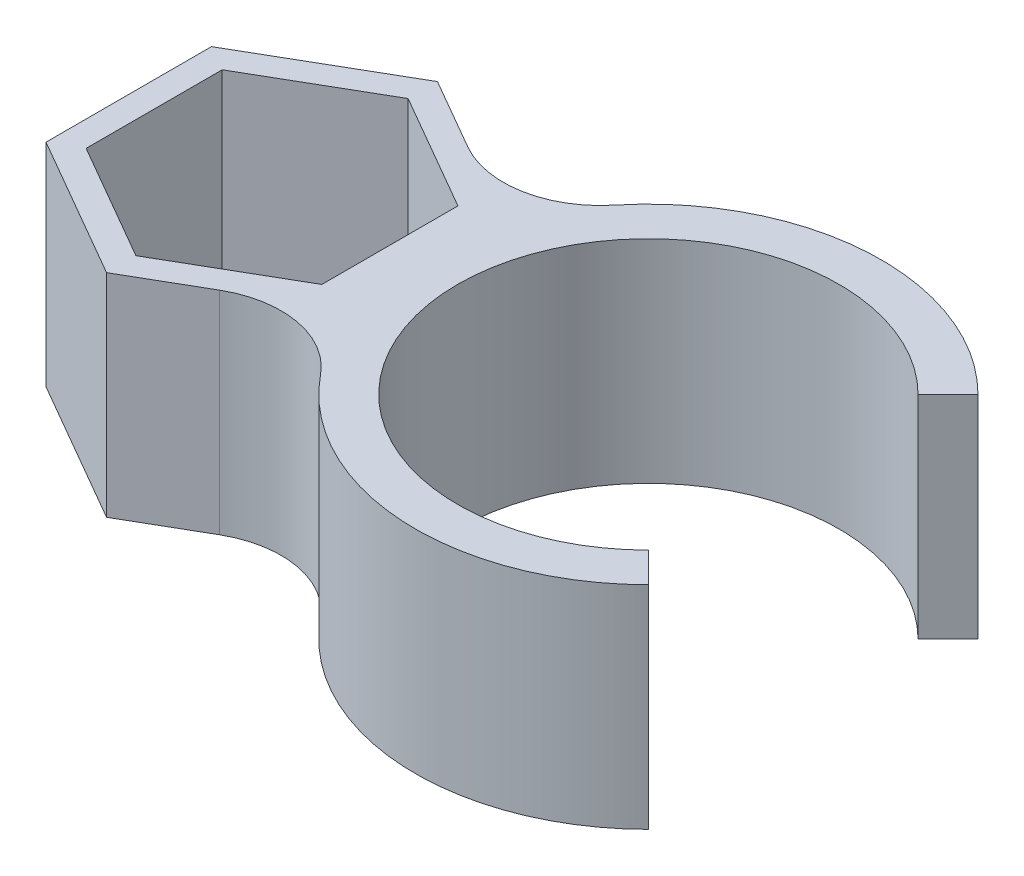
SolidWorks part; units mm, degrees
ref_plane "Front Plane" through (0, 0, 0) normal (0, 0, 1) x (1, 0, 0)
ref_plane "Top Plane" through (0, 0, 0) normal (0, 1, 0) x (1, 0, 0)
ref_plane "Right Plane" through (0, 0, 0) normal (1, 0, 0) x (0, 0, -1)
sketch "Sketch1" plane through (0, 0, 0) normal (0, 1, 0) x (1, 0, 0)
  line L0 (15.8637, -1.8989) -> (35353.1257, 35335.3631) construction
  line L1 (5.5626, 3.2116) -> (0, 6.4231)
  line L2 (0, 6.4231) -> (-5.5626, 3.2116)
  line L3 (-5.5626, 3.2116) -> (-5.5626, -3.2116)
  line L4 (-5.5626, -3.2116) -> (0, -6.4231)
  line L5 (0, -6.4231) -> (5.5626, -3.2116)
  line L6 (5.5626, -3.2116) -> (5.5626, 3.2116)
  line L7 (0, 0) -> (10412.92, 0) construction
  line L8 (15.8637, 1.8989) -> (35353.1257, -35335.3631) construction
  line L9 (24.1266, 6.364) -> (25.5408, 7.7782)
  line L10 (24.1266, -6.364) -> (25.5408, -7.7782)
  line L12 (6.7626, 3.9044) -> (0, 7.8088)
  line L13 (0, 7.8088) -> (-6.7626, 3.9044)
  line L14 (-6.7626, 3.9044) -> (-6.7626, -3.9044)
  line L15 (-6.7626, -3.9044) -> (0, -7.8088)
  line L16 (0, -7.8088) -> (6.7626, -3.9044)
  line L17 (6.7626, -3.9044) -> (6.7626, 3.9044)
  circle A0 centre (0, 0) radius 5.5626 construction
  arc A1 (24.1266, 6.364) -> (24.1266, -6.364) centre (17.7626, 0) ccw
  arc A2 (25.5408, 7.7782) -> (25.5408, -7.7782) centre (17.7626, 0) ccw
  circle A3 centre (0, 0) radius 6.7626 construction
  arc A4 (3.3813, 5.8566) -> (9.2242, 6.9351) centre (5.6704, 9.8215) ccw
  arc A5 (3.3813, -5.8566) -> (9.2242, -6.9351) centre (5.6704, -9.8215) cw
  dimension "D3" = 9
  dimension "D6" = 1.2
  dimension "D1" = 11.1252
  dimension "D2" = 90
  dimension "D4" = 2
  dimension "D5" = 45
extrude "Boss-Extrude1" add sketch "Sketch1" along normal blind 10 contours L16 L17 L12 L13 L14 L15 L6 L5 L4 L3 L2 L1 | L16 A5 A2 L17 | A4 L12 L17 A2 | L9 A2 L10 A1
